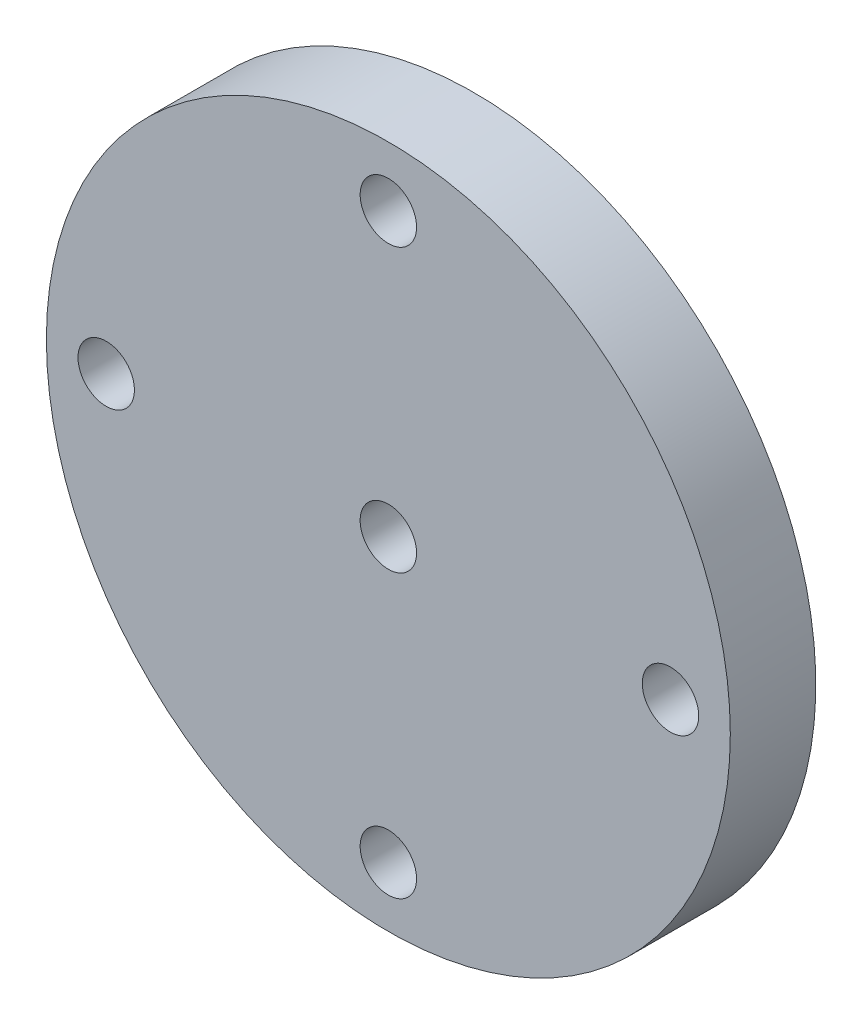
SolidWorks part; units mm, degrees
material "6061 Alloy"
ref_plane "Front Plane" through (0, 0, 0) normal (0, 0, 1) x (1, 0, 0)
ref_plane "Top Plane" through (0, 0, 0) normal (0, 1, 0) x (1, 0, 0)
ref_plane "Right Plane" through (0, 0, 0) normal (1, 0, 0) x (0, 0, -1)
sketch "Sketch1" plane through (0, 0, 0) normal (0, 0, 1) x (1, 0, 0)
  circle A0 centre (0, 0) radius 20
  dimension "D1" = 40
extrude "Boss-Extrude1" add sketch "Sketch1" along normal blind 10
sketch "Sketch2" plane through (0, 0, 0) normal (0, 0, -1) x (-1, 0, 0)
  line L1 (-5, -5) -> (5, -5)
  line L2 (-5, -5) -> (-5, 5)
  line L3 (-5, 5) -> (5, 5)
  line L4 (5, -5) -> (5, 5)
  line L5 (-5, -5) -> (5, 5) construction
  line L6 (-5, 5) -> (5, -5) construction
  point P0 (0, 0)
  dimension "D1" = 10
  dimension "D2" = 10
extrude "Cut-Extrude1" cut sketch "Sketch2" against normal blind 5
hole_wizard "M4x0.7 Tapped Hole1" positions "Sketch4" profile "Sketch5" tap size "M4x0.7" standard "ANSI Metric" end condition through all
sketch "Sketch4" plane through (0, 0, 10) normal (0, 0, 1) x (1, 0, 0)
  point P0 (0, 0)
sketch "Sketch5" plane through (0, 0, 10) normal (1, 0, 0) x (0, -1, 0)
  line L0 (0, 0) -> (0, 10)
  line L1 (0, 10) -> (1.65, 10)
  line L2 (1.65, 10) -> (1.65, 0)
  line L5 (1.65, 0) -> (0, 0)
  line L11 (0, -6.35) -> (0, 107.95) construction
  dimension "Thread Major Dia." = 3.3
  dimension "Thru Tap Drill Depth" = 10
sketch "Sketch6" plane through (0, 0, 0) normal (0, 0, -1) x (-1, 0, 0)
  circle A0 centre (0, 0) radius 12.5
  circle A1 centre (0, 0) radius 20
  dimension "D1" = 25
  dimension "D2" = 40
extrude "Cut-Extrude2" cut sketch "Sketch6" against normal blind 5
hole_wizard "M4x0.7 Tapped Hole2" positions "Sketch7" profile "Sketch8" tap size "M4x0.7" standard "ANSI Metric" end condition through all
sketch "Sketch7" plane through (0, 0, 5) normal (0, 0, -1) x (-1, 0, 0)
  line L0 (0, 5.5) -> (0, -5.5) construction
  line L1 (5.5, 0) -> (-5.5, 0) construction
  circle A0 centre (0, 0) radius 16.5
  point P0 (0, 16.5)
  point P4 (16.5, 0)
  point P8 (0, -16.5)
  point P10 (0, 0)
  point P15 (-16.5, 0)
  point P23 (0, 0)
  point P24 (0, 0)
  dimension "D1" = 33
sketch "Sketch8" plane through (0, 16.5, 5) normal (1, 0, 0) x (0, 1, 0)
  line L0 (0, 0) -> (0, 5)
  line L1 (0, 5) -> (1.65, 5)
  line L2 (1.65, 5) -> (1.65, 0)
  line L5 (1.65, 0) -> (0, 0)
  line L11 (0, -6.35) -> (0, 107.95) construction
  dimension "Thread Major Dia." = 3.3
  dimension "Thru Tap Drill Depth" = 5
